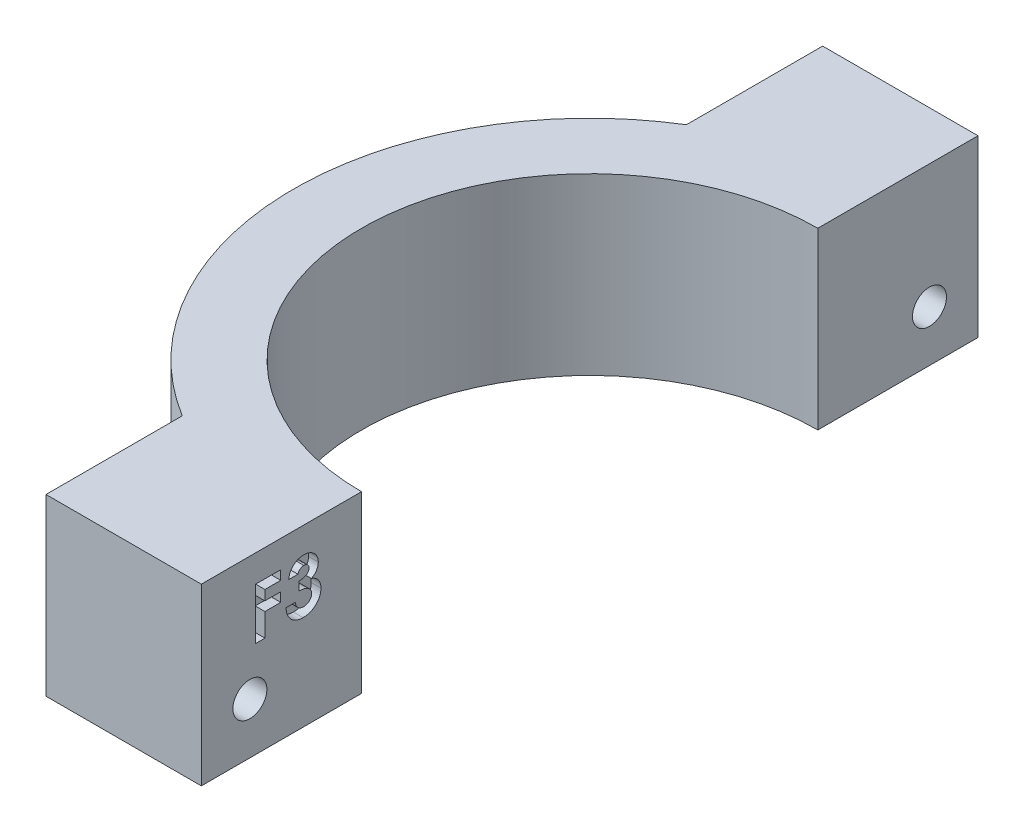
SolidWorks part; units mm, degrees
ref_plane "Front Plane" through (0, 0, 0) normal (0, 0, 1) x (1, 0, 0)
ref_plane "Top Plane" through (0, 0, 0) normal (0, 1, 0) x (1, 0, 0)
ref_plane "Right Plane" through (0, 0, 0) normal (1, 0, 0) x (0, 0, -1)
sketch "Sketch1" plane through (0, 0, 0) normal (0, 1, 0) x (1, 0, 0)
  line L0 (-48.9983, 32.5286) -> (-48.9983, -47.4714)
  line L1 (-48.9983, -47.4714) -> (-16.9983, -47.4714)
  line L2 (-16.9983, -47.4714) -> (-16.9983, -30.9714)
  line L3 (-48.9983, 32.5286) -> (-16.9983, 32.5286)
  line L4 (-16.9983, 32.5286) -> (-16.9983, 16.0286)
  line L5 (-32.9983, 32.5286) -> (-32.9983, 18.4949)
  line L6 (-32.9983, -47.4714) -> (-32.9983, -33.4378)
  arc A0 (-16.9983, 16.0286) -> (-16.9983, -30.9714) centre (-16.9983, -7.4714) ccw
  arc A1 (-16.9983, 23.0286) -> (-16.9983, -37.9714) centre (-16.9983, -7.4714) ccw
  point P14 (0, 0)
  point P15 (-32.5785, -30.9714)
  point P16 (-32.9983, -33.4378)
  dimension "D1" = 80
  dimension "D2" = 32
  dimension "D3" = 32
  dimension "D4" = 16.5
  dimension "D5" = 16.5
  dimension "D6" = 47
  dimension "D7" = 7
extrude "Boss-Extrude1" add sketch "Sketch1" along normal blind 18 contours A1 L4 L3 L5 | L4 A1 L0 L2 A0 | A1 L6 L1 L2
sketch "Sketch2" plane through (-16.9983, 0, 0) normal (1, 0, 0) x (0, 0, -1)
  line L0 (-47.4714, 18) -> (-47.4714, 0) construction
  line L3 (32.5286, 18) -> (32.5286, 0) construction
  line L8 (32.5286, 18) -> (16.0286, 18) construction
  line L9 (-47.4714, 18) -> (-30.9714, 18) construction
  circle A0 centre (-42.4714, 5.25) radius 1.75
  circle A1 centre (27.5286, 5.25) radius 1.75
  point P10 (0, 0)
  dimension "D3" = 12.75
  dimension "D5" = 3.5
  dimension "D6" = 3.5
  dimension "D1" = 5
  dimension "D2" = 5
  dimension "D4" = 12.75
extrude "Cut-Extrude1" cut sketch "Sketch2" against normal through all
sketch "Sketch3" plane through (-16.9983, 0, 0) normal (1, 0, 0) x (0, 0, -1)
  text T0 "<b>F3</b>" font "Century Gothic" height in points 20
extrude "Cut-Extrude2" cut sketch "Sketch3" against normal blind 1
sketch "Sketch4" plane through (-32.9983, 0, 0) normal (-1, 0, 0) x (0, 0, 1)
  line L1 (-25.5288, 2.7834) -> (-24.3925, 5.7486)
  line L2 (-24.3925, 5.7486) -> (-26.3923, 8.2152)
  line L3 (-26.3923, 8.2152) -> (-29.5284, 7.7166)
  line L4 (-29.5284, 7.7166) -> (-30.6646, 4.7514)
  line L5 (-30.6646, 4.7514) -> (-28.6648, 2.2848)
  line L6 (-28.6648, 2.2848) -> (-25.5288, 2.7834)
  line L7 (44.3628, 2.6993) -> (45.6261, 5.6126)
  line L8 (45.6261, 5.6126) -> (43.7347, 8.1633)
  line L9 (43.7347, 8.1633) -> (40.5801, 7.8007)
  line L10 (40.5801, 7.8007) -> (39.3168, 4.8874)
  line L11 (39.3168, 4.8874) -> (41.2081, 2.3367)
  line L12 (41.2081, 2.3367) -> (44.3628, 2.6993)
  circle A0 centre (-27.5286, 5.25) radius 2.75 construction
  circle A1 centre (42.4714, 5.25) radius 2.75 construction
extrude "Cut-Extrude3" cut sketch "Sketch4" against normal blind 5
